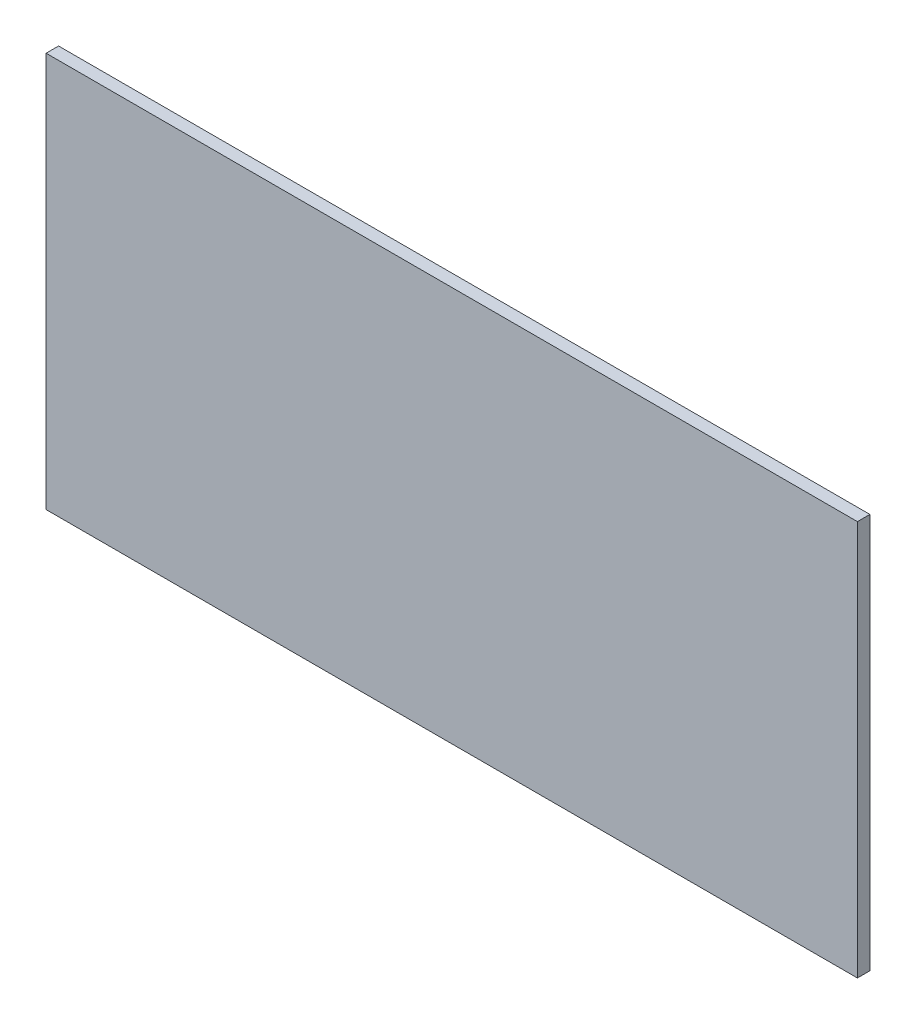
SolidWorks part; units mm, degrees
ref_plane "Plan de face" through (0, 0, 0) normal (0, 0, 1) x (1, 0, 0)
ref_plane "Plan de dessus" through (0, 0, 0) normal (0, 1, 0) x (1, 0, 0)
ref_plane "Plan de droite" through (0, 0, 0) normal (1, 0, 0) x (0, 0, -1)
sketch "Esquisse1" plane through (0, 0, 0) normal (0, 0, 1) x (1, 0, 0)
  line L1 (0, 0) -> (195, 0)
  line L2 (0, 0) -> (0, 95)
  line L3 (0, 95) -> (195, 95)
  line L4 (195, 0) -> (195, 95)
  dimension "D1" = 95
  dimension "D2" = 195
extrude "Boss.-Extru.1" add sketch "Esquisse1" along normal blind 3
